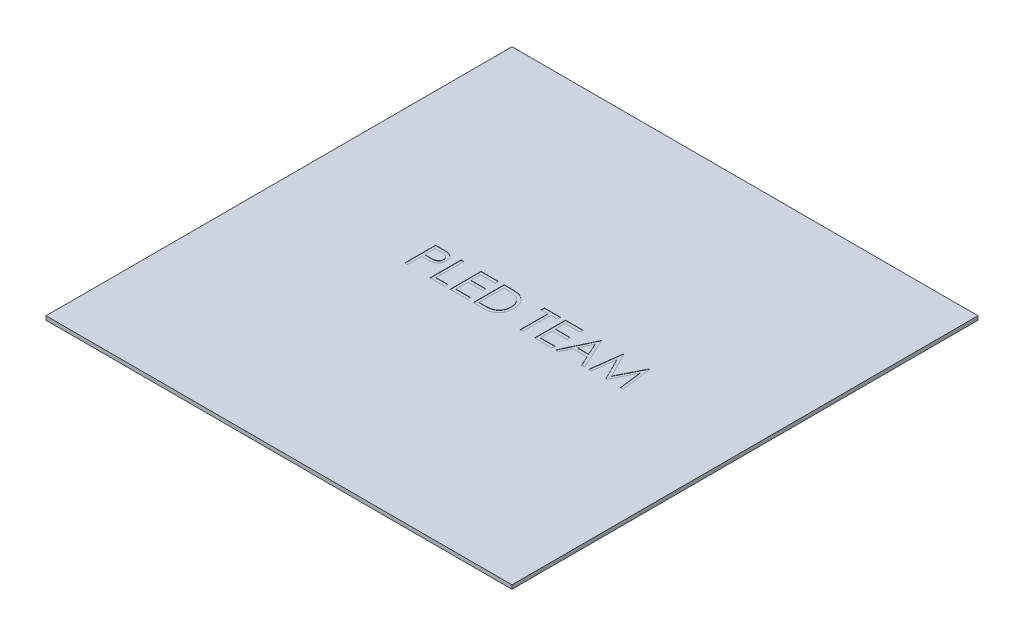
SolidWorks part; units mm, degrees
ref_plane "Front Plane" through (0, 0, 0) normal (0, 0, 1) x (1, 0, 0)
ref_plane "Top Plane" through (0, 0, 0) normal (0, 1, 0) x (1, 0, 0)
ref_plane "Right Plane" through (0, 0, 0) normal (1, 0, 0) x (0, 0, -1)
sketch "Sketch1" plane through (0, 0, 0) normal (0, 1, 0) x (1, 0, 0)
  line L1 (190.5, -190.5) -> (-190.5, -190.5)
  line L2 (190.5, -190.5) -> (190.5, 190.5)
  line L3 (190.5, 190.5) -> (-190.5, 190.5)
  line L4 (-190.5, -190.5) -> (-190.5, 190.5)
  line L5 (190.5, -190.5) -> (-190.5, 190.5) construction
  line L6 (190.5, 190.5) -> (-190.5, -190.5) construction
  point P0 (0, 0)
extrude "Boss-Extrude1" add sketch "Sketch1" along normal blind 3.175
sketch "Sketch3" plane through (0, 3.175, 0) normal (0, 1, 0) x (1, 0, 0)
  text T0 "PLED TEAM" font "Century Gothic" height 25.4
extrude "Cut-Extrude1" cut sketch "Sketch3" against normal blind 0.254
